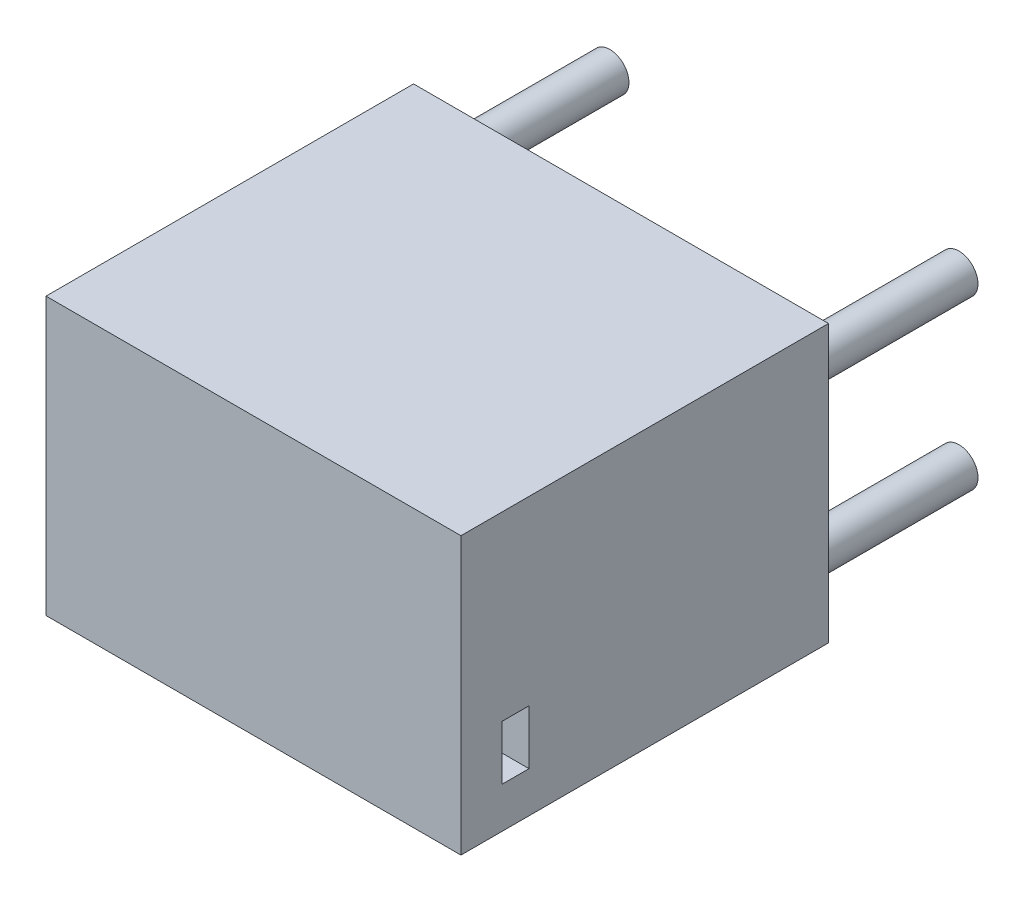
SolidWorks part; units mm, degrees
ref_plane "Front Plane" through (0, 0, 0) normal (0, 0, 1) x (1, 0, 0)
ref_plane "Top Plane" through (0, 0, 0) normal (0, 1, 0) x (1, 0, 0)
ref_plane "Right Plane" through (0, 0, 0) normal (1, 0, 0) x (0, 0, -1)
sketch "Sketch1" plane through (0, 0, 0) normal (0, 0, 1) x (1, 0, 0)
  line L1 (76.2, -50.8) -> (-76.2, -50.8)
  line L2 (76.2, -50.8) -> (76.2, 50.8)
  line L3 (76.2, 50.8) -> (-76.2, 50.8)
  line L4 (-76.2, -50.8) -> (-76.2, 50.8)
  line L5 (76.2, -50.8) -> (-76.2, 50.8) construction
  line L6 (76.2, 50.8) -> (-76.2, -50.8) construction
  point P0 (0, 0)
  dimension "D1" = 101.6
  dimension "D2" = 152.4
extrude "Boss-Extrude1" add sketch "Sketch1" along normal blind 135
sketch "Sketch2" plane through (0, 0, 0) normal (0, 0, -1) x (-1, 0, 0)
  line L1 (52, -39) -> (-52, -39)
  line L2 (52, -39) -> (52, 39)
  line L3 (52, 39) -> (-52, 39)
  line L4 (-52, -39) -> (-52, 39)
  line L5 (52, -39) -> (-52, 39) construction
  line L6 (52, 39) -> (-52, -39) construction
  point P0 (0, 0)
  dimension "D1" = 104
  dimension "D2" = 78
extrude "Cut-Extrude1" cut sketch "Sketch2" against normal blind 6
sketch "Sketch4" plane through (0, 0, 0) normal (0, 0, -1) x (-1, 0, 0)
  line L0 (-76.2, -50.8) -> (-76.2, 50.8) construction
  line L1 (-76.2, 50.8) -> (76.2, 50.8) construction
  line L2 (76.2, -50.8) -> (-76.2, -50.8) construction
  line L3 (76.2, 50.8) -> (76.2, -50.8) construction
  circle A0 centre (-64.1, -30.8) radius 7
  circle A1 centre (-64.1, 30.8) radius 7
  circle A2 centre (64.1, 30.8) radius 7
  circle A3 centre (64.1, -30.8) radius 7
  dimension "D1" = 14
  dimension "D2" = 14
  dimension "D3" = 14
  dimension "D4" = 14
  dimension "D5" = 12.1
  dimension "D8" = 20
  dimension "D10" = 20
  dimension "D11" = 12.1
  dimension "D12" = 20
  dimension "D6" = 20
  dimension "D7" = 12.1
  dimension "D9" = 12.1
extrude "Boss-Extrude3" add sketch "Sketch4" along normal blind 60
sketch "Sketch5" plane through (0, 0, -60) normal (0, 0, -1) x (-1, 0, 0)
  circle A0 centre (-64.1, 30.8) radius 4.5
  circle A1 centre (64.1, 30.8) radius 4.5
  circle A2 centre (64.1, -30.8) radius 4.5
  circle A3 centre (-64.1, -30.8) radius 4.5
  dimension "D1" = 9
  dimension "D2" = 9
  dimension "D3" = 9
  dimension "D4" = 9
extrude "Cut-Extrude3" cut sketch "Sketch5" against normal blind 80
sketch "Sketch12" plane through (0, 0, 6) normal (0, 0, -1) x (-1, 0, 0)
  line L1 (50, -37.75) -> (-50, -37.75)
  line L2 (50, -37.75) -> (50, 37.75)
  line L3 (50, 37.75) -> (-50, 37.75)
  line L4 (-50, -37.75) -> (-50, 37.75)
  line L5 (50, -37.75) -> (-50, 37.75) construction
  line L6 (50, 37.75) -> (-50, -37.75) construction
  point P0 (0, 0)
  dimension "D1" = 100
  dimension "D2" = 75.5
extrude "Cut-Extrude7" cut sketch "Sketch12" against normal blind 120
sketch "Sketch13" plane through (0, 0, 126) normal (0, 0, -1) x (-1, 0, 0)
  line L0 (50, 37.75) -> (-50, 37.75) construction
  line L1 (30, -16.25) -> (-30, -16.25)
  line L2 (30, -16.25) -> (30, 25.75)
  line L3 (30, 25.75) -> (-30, 25.75)
  line L4 (-30, -16.25) -> (-30, 25.75)
  point P0 (0, 0)
  dimension "D1" = 60
  dimension "D2" = 42
  dimension "D3" = 12
extrude "Cut-Extrude8" cut sketch "Sketch13" against normal blind 2
sketch "Sketch24" plane through (50, 0, 0) normal (-1, 0, 0) x (0, 0, 1)
  line L0 (0, 37.8) -> (0, 23.8) construction
  circle A0 centre (12.5, 30.8) radius 2.5
  circle A1 centre (12.5, -30.8) radius 2.5
  dimension "D1" = 5
  dimension "D2" = 12.5
  dimension "D3" = 5
extrude "Cut-Extrude9" cut sketch "Sketch24" against normal blind 15
mirror "Mirror2" about plane through (0, 0, 0) normal (1, 0, 0) of "Cut-Extrude9"
sketch "Sketch26" plane through (50, 0, 0) normal (-1, 0, 0) x (0, 0, 1)
  line L0 (135, 50.8) -> (135, -50.8) construction
  line L1 (110, -15.8) -> (120, -15.8)
  line L2 (110, -15.8) -> (110, -35.8)
  line L3 (110, -35.8) -> (120, -35.8)
  line L4 (120, -15.8) -> (120, -35.8)
  line L5 (135, -50.8) -> (0, -50.8) construction
  dimension "D1" = 10
  dimension "D2" = 15
  dimension "D3" = 20
  dimension "D4" = 15
extrude "Cut-Extrude10" cut sketch "Sketch26" against normal through all
